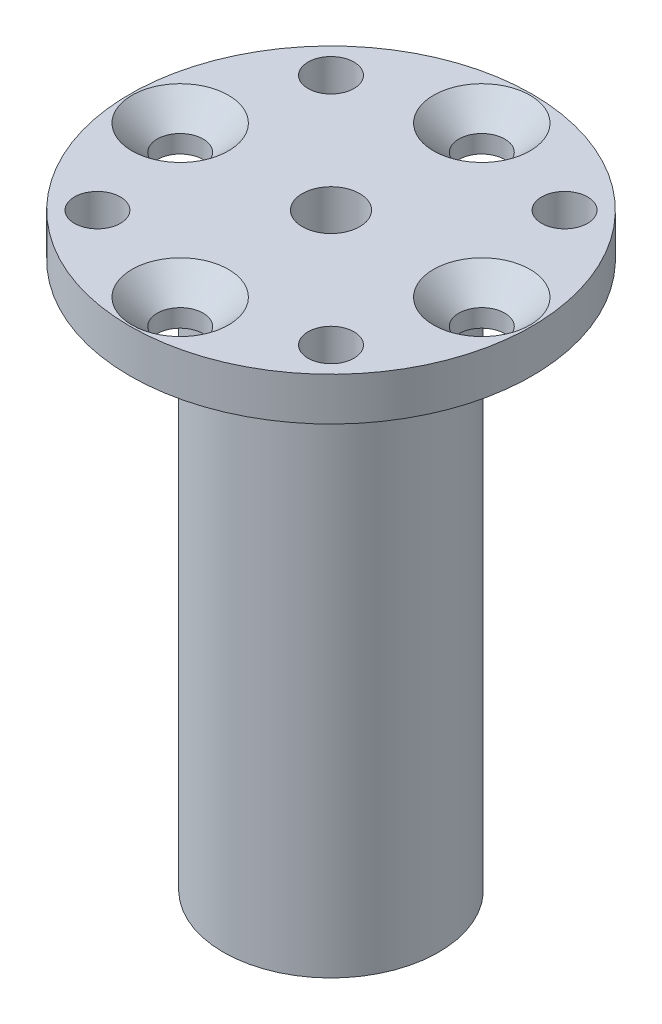
SolidWorks part; units mm, degrees
ref_plane "Ebene vorne" through (0, 0, 0) normal (0, 0, 1) x (1, 0, 0)
ref_plane "Ebene oben" through (0, 0, 0) normal (0, 1, 0) x (1, 0, 0)
ref_plane "Ebene rechts" through (0, 0, 0) normal (1, 0, 0) x (0, 0, -1)
sketch "Skizze1" plane through (0, 0, 0) normal (0, 0, 1) x (1, 0, 0)
  line L0 (0, 9.4149) -> (0, -43.1354) construction
  line L1 (0, 0) -> (14, 0)
  line L2 (14, 0) -> (14, -3)
  line L3 (14, -3) -> (7.5, -3)
  line L4 (7.5, -3) -> (7.5, -41)
  line L5 (7.5, -41) -> (0, -41)
  line L6 (0, -41) -> (0, 0)
  dimension "D1" = 15
  dimension "D2" = 38
  dimension "D3" = 41
  dimension "D4" = 28
revolve "Rotation1" add sketch "Skizze1" angle 360 about L0
hole_wizard "Ø4.0 (4) Durchmesser Bohrung1" positions "Skizze3" profile "Skizze2" hole size "Ø4.0" standard "ISO" end condition up to next
sketch "Skizze3" plane through (0, 0, 0) normal (0, 1, 0) x (1, 0, 0)
  point P0 (0, 0)
sketch "Skizze2" plane through (0, 0, 0) normal (1, 0, 0) x (0, 0, 1)
  line L0 (0, 0) -> (0, 41)
  line L1 (0, 41) -> (2, 41)
  line L2 (2, 41) -> (2, 0)
  line L5 (2, 0) -> (0, 0)
  line L11 (0, -6.35) -> (0, 107.95) construction
  dimension "Bohrerdurchmesser" = 4
  dimension "Bohrungstiefe" = 41
hole_wizard "M3 Gewindebohrung1" positions "Skizze5" profile "Skizze4" tap size "M3" standard "ISO"
sketch "Skizze5" plane through (0, -41, 0) normal (0, -1, 0) x (-1, 0, 0)
  point P0 (-5.5, 0)
  dimension "D1" = 5.5
sketch "Skizze4" plane through (5.5, -41, 0) normal (1, 0, 0) x (0, 0, -1)
  line L0 (0, 0) -> (0, 12.7511)
  line L1 (0, 12.7511) -> (1.25, 12)
  line L2 (1.25, 12) -> (1.25, 0)
  line L5 (1.25, 0) -> (0, 0)
  line L10 (0, 12.7511) -> (-1.25, 12) construction
  line L11 (0, -6.35) -> (0, 107.95) construction
  dimension "Bohrerdurchmesser" = 2.5
  dimension "Bohrungstiefe" = 12
  dimension "Spitzenwinkel" = 118
cosmetic thread "Bohrungsgewinde1" parameters "D1"=10, "D2"=3
pattern_circular "Kreismuster1" count 3 over 360 about axis through (0, 0, 0) along (0, 1, 0) of "M3 Gewindebohrung1"
hole_wizard "Formsenkung für M3 Senkschraube mit Innensechskant1" positions "Skizze7" profile "Skizze6" countersink size "M3" standard "ISO" end condition up to next
sketch "Skizze7" plane through (0, 0, 0) normal (0, 1, 0) x (1, 0, 0)
  point P0 (0, 10.5)
  dimension "D1" = 10.5
sketch "Skizze6" plane through (0, 0, -10.5) normal (1, 0, 0) x (0, 0, 1)
  line L0 (0, 0) -> (0, 3.001)
  line L1 (0, 3.001) -> (1.6, 3.001)
  line L2 (1.6, 3.001) -> (1.6, 1.76)
  line L3 (1.6, 1.76) -> (3.36, 0)
  line L5 (3.36, 0) -> (0, 0)
  line L6 (-1.6, 1.76) -> (-3.36, 0) construction
  line L11 (0, -6.35) -> (0, 107.95) construction
  dimension "Bohrerdurchmesser" = 3.2
  dimension "Bohrungstiefe" = 3.001
  dimension "Senkdurchmesser (Oben)" = 6.72
  dimension "Senkwinkel (Oben)" = 90
pattern_circular "Kreismuster2" count 4 over 360 about axis through (0, 0, 0) along (0, 1, 0) of "Formsenkung für M3 Senkschraube mit Innensechskant1"
hole_wizard "Ø3.2 (3.2) Durchmesser Bohrung1" positions "Skizze9" profile "Skizze10" hole size "Ø3.2" standard "ISO" end condition up to next
sketch "Skizze9" plane through (0, 0, 0) normal (0, 1, 0) x (1, 0, 0)
  line L0 (-12.965, 0) -> (0, 0) construction
  line L1 (0, 0) -> (-8.1317, 8.1317) construction
  point P0 (-8.1317, 8.1317)
  dimension "D1" = 45
  dimension "D2" = 11.5
sketch "Skizze10" plane through (-8.1317, 0, -8.1317) normal (1, 0, 0) x (0, 0, 1)
  line L0 (0, 0) -> (0, 3.001)
  line L1 (0, 3.001) -> (1.6, 3.001)
  line L2 (1.6, 3.001) -> (1.6, 0)
  line L5 (1.6, 0) -> (0, 0)
  line L11 (0, -6.35) -> (0, 107.95) construction
  dimension "Bohrerdurchmesser" = 3.2
  dimension "Bohrungstiefe" = 3.001
pattern_circular "Kreismuster3" count 4 over 360 about axis through (0, 0, 0) along (0, 1, 0) of "Ø3.2 (3.2) Durchmesser Bohrung1"
